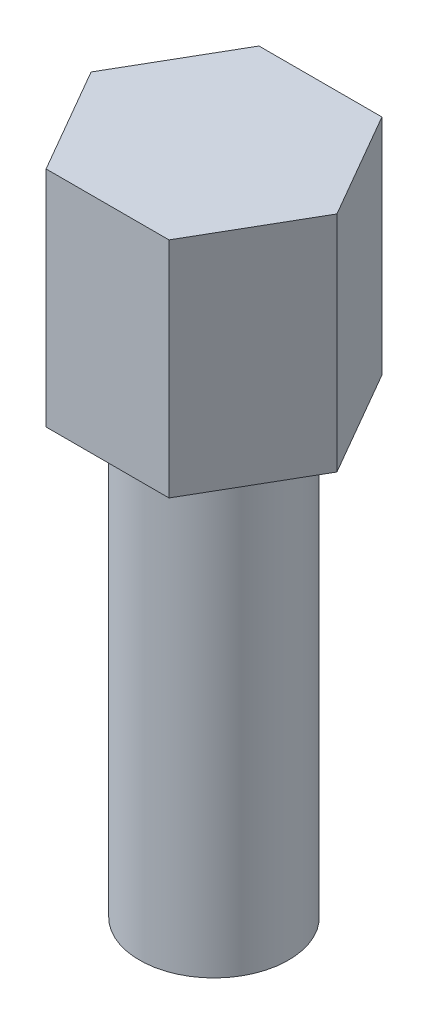
SolidWorks part; units mm, degrees
ref_plane "Front Plane" through (0, 0, 0) normal (0, 0, 1) x (1, 0, 0)
ref_plane "Top Plane" through (0, 0, 0) normal (0, 1, 0) x (1, 0, 0)
ref_plane "Right Plane" through (0, 0, 0) normal (1, 0, 0) x (0, 0, -1)
sketch "Sketch1" plane through (0, 0, 0) normal (0, 1, 0) x (1, 0, 0)
  line L1 (1.65, 0) -> (0.825, 1.4289)
  line L2 (0.825, 1.4289) -> (-0.825, 1.4289)
  line L3 (-0.825, 1.4289) -> (-1.65, 0)
  line L4 (-1.65, 0) -> (-0.825, -1.4289)
  line L5 (-0.825, -1.4289) -> (0.825, -1.4289)
  line L6 (0.825, -1.4289) -> (1.65, 0)
  circle A0 centre (0, 0) radius 1.65 construction
extrude "Boss-Extrude1" add sketch "Sketch1" along normal blind 3
sketch "Sketch2" plane through (0, 0, 0) normal (0, -1, 0) x (1, 0, 0)
  circle A0 centre (0, 0) radius 1
extrude "Boss-Extrude2" add sketch "Sketch2" along normal blind 6
